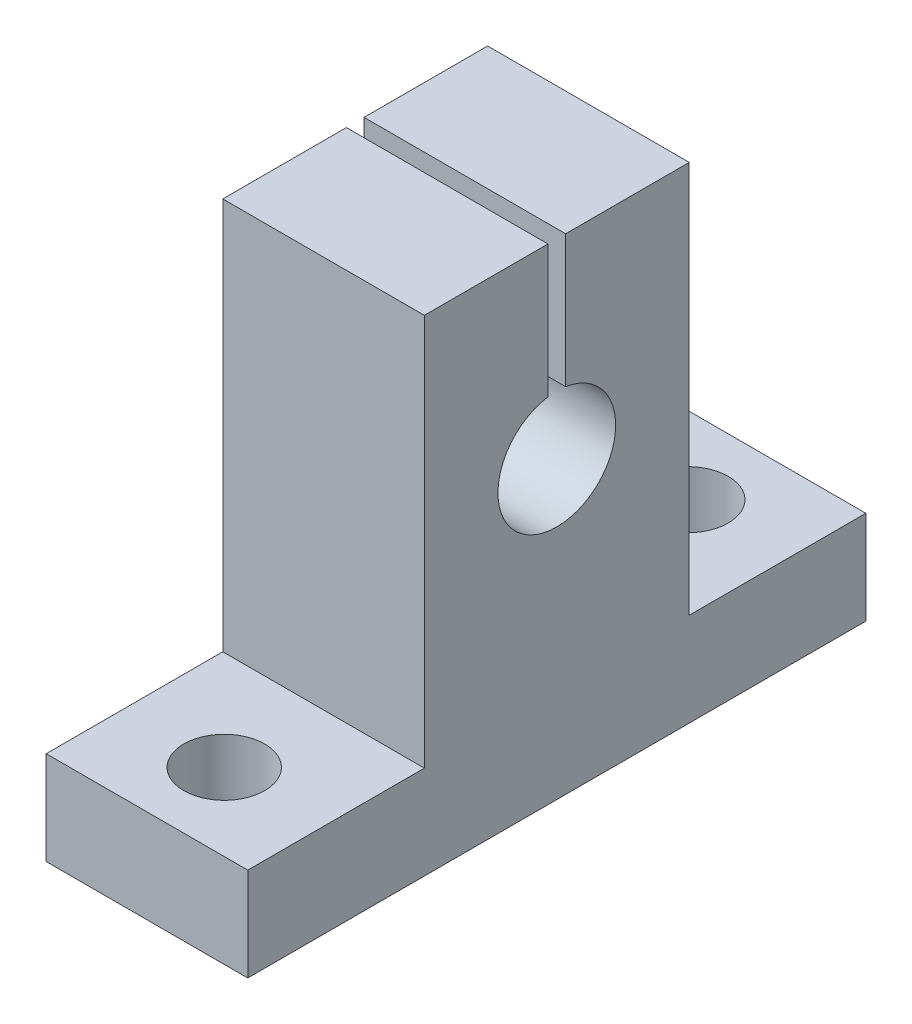
SolidWorks part; units mm, degrees
material "2014-O"
ref_plane "Front Plane" through (0, 0, 0) normal (0, 0, 1) x (1, 0, 0)
ref_plane "Top Plane" through (0, 0, 0) normal (0, 1, 0) x (1, 0, 0)
ref_plane "Right Plane" through (0, 0, 0) normal (1, 0, 0) x (0, 0, -1)
sketch "Sketch1" plane through (0, 0, 0) normal (0, 1, 0) x (1, 0, 0)
  line L1 (-6.85, -21) -> (6.85, -21)
  line L2 (-6.85, -21) -> (-6.85, 21)
  line L3 (-6.85, 21) -> (6.85, 21)
  line L4 (6.85, -21) -> (6.85, 21)
  line L5 (-6.85, -21) -> (6.85, 21) construction
  line L6 (-6.85, 21) -> (6.85, -21) construction
  point P0 (0, 0)
  dimension "D1" = 13.7
  dimension "D2" = 42
extrude "Boss-Extrude1" add sketch "Sketch1" along normal blind 6.35 contours L3 L4 L1 L2
sketch "Sketch2" plane through (0, 6.35, 0) normal (0, 1, 0) x (1, 0, 0)
  line L0 (6.85, -21) -> (6.85, 21) construction
  line L1 (-6.85, -9) -> (6.85, -9)
  line L2 (-6.85, -9) -> (-6.85, 9)
  line L3 (-6.85, 9) -> (6.85, 9)
  line L4 (6.85, -9) -> (6.85, 9)
  line L5 (-6.85, -9) -> (6.85, 9) construction
  line L6 (-6.85, 9) -> (6.85, -9) construction
  point P0 (0, 0)
  dimension "D1" = 18
extrude "Boss-Extrude2" add sketch "Sketch2" along normal blind 26.65
sketch "Sketch3" plane through (-6.85, 0, 0) normal (-1, 0, 0) x (0, 0, 1)
  line L0 (-9, 33) -> (9, 33) construction
  line L2 (-0.6, 24) -> (-0.6, 33)
  line L3 (-0.6, 33) -> (0.6, 33)
  line L4 (0.6, 24) -> (0.6, 33)
  line L5 (-0.6, 24) -> (0.6, 33) construction
  line L6 (-0.6, 33) -> (0.6, 24) construction
  arc A0 (-0.6, 24) -> (0.6, 24) centre (0, 20.0453) ccw
  point P0 (0, 28.5)
  dimension "D1" = 4
  dimension "D2" = 1.2
  dimension "D3" = 0.6
  dimension "D4" = 9
extrude "Cut-Extrude1" cut sketch "Sketch3" against normal through all
sketch "Sketch4" plane through (0, 6.35, 0) normal (0, 1, 0) x (1, 0, 0)
  line L0 (-6.85, -21) -> (6.85, -21) construction
  circle A0 centre (0, -15.75) radius 2.75
  point P2 (0, -21)
  dimension "D1" = 5.5
  dimension "D2" = 5.25
extrude "Cut-Extrude2" cut sketch "Sketch4" against normal through all
mirror "Mirror1" about plane through (0, 0, 0) normal (0, 0, 1) of "Cut-Extrude2"
